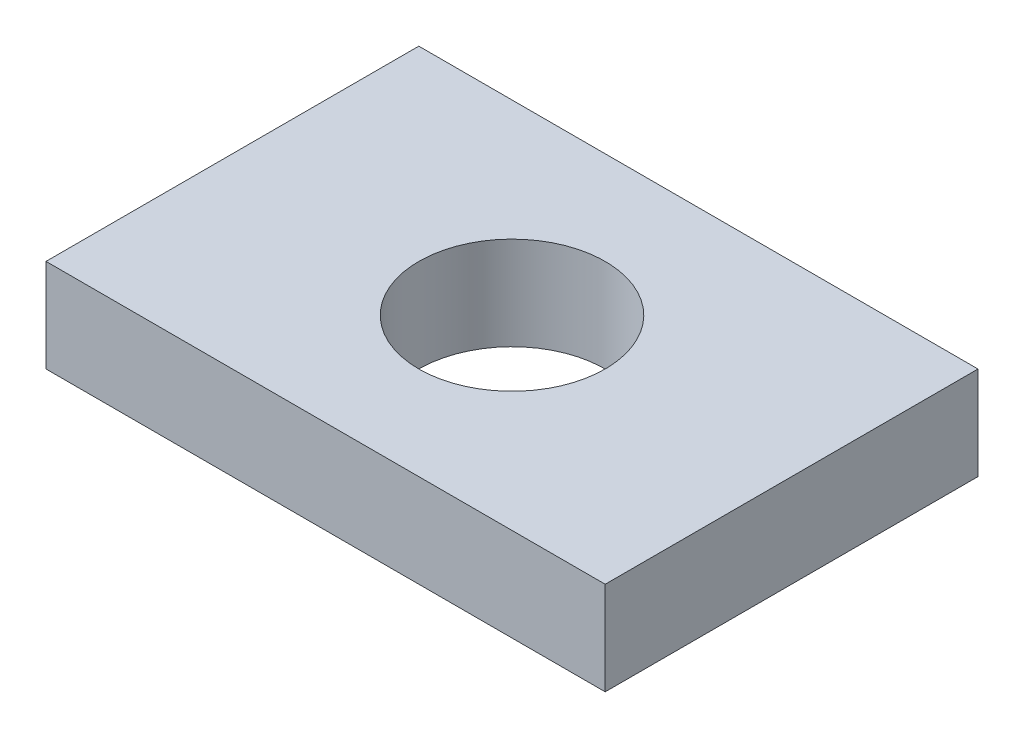
SolidWorks part; units mm, degrees
ref_plane "Front Plane" through (0, 0, 0) normal (0, 0, 1) x (1, 0, 0)
ref_plane "Top Plane" through (0, 0, 0) normal (0, 1, 0) x (1, 0, 0)
ref_plane "Right Plane" through (0, 0, 0) normal (1, 0, 0) x (0, 0, -1)
sketch "Sketch1" plane through (0, 0, 0) normal (0, 1, 0) x (1, 0, 0)
  line L1 (0, 0) -> (38.1, 0)
  line L2 (0, 0) -> (0, 25.4)
  line L3 (0, 25.4) -> (38.1, 25.4)
  line L4 (38.1, 0) -> (38.1, 25.4)
  circle A0 centre (19.05, 12.7) radius 6.35
  point P7 (19.05, 25.4)
  point P8 (0, 12.7)
  point P9 (0, 0)
  point P10 (0, 0)
  dimension "D1" = 12.7
  dimension "D2" = 38.1
  dimension "D3" = 25.4
extrude "Boss-Extrude1" add sketch "Sketch1" along normal blind 6.35
